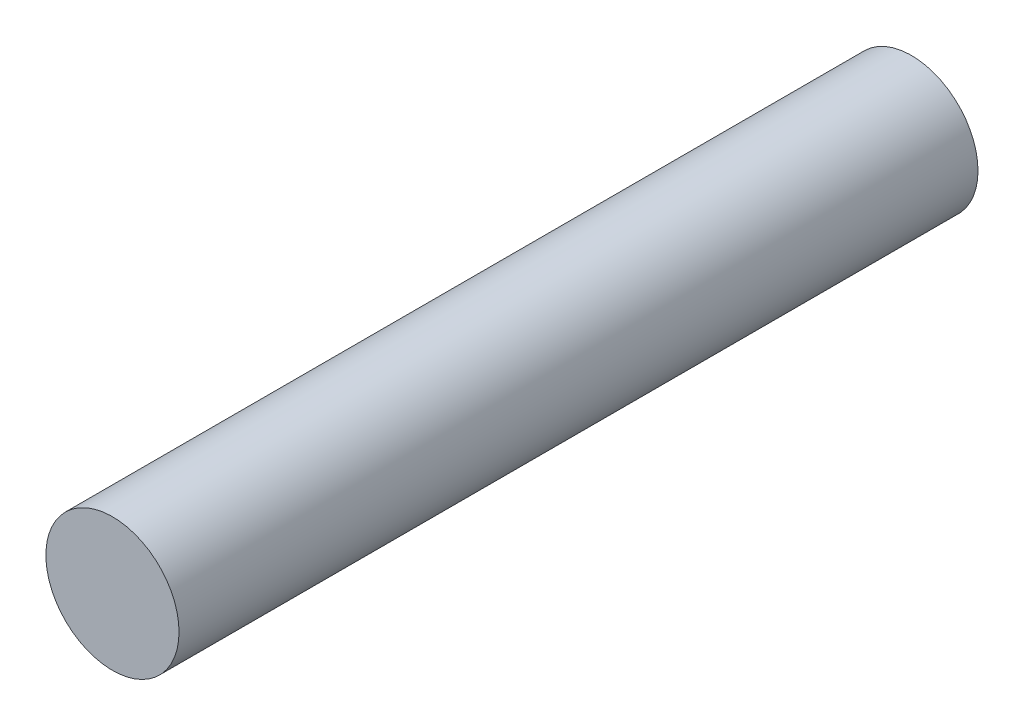
SolidWorks part; units mm, degrees
ref_plane "前基準面" through (0, 0, 0) normal (0, 0, 1) x (1, 0, 0)
ref_plane "上基準面" through (0, 0, 0) normal (0, 1, 0) x (1, 0, 0)
ref_plane "右基準面" through (0, 0, 0) normal (1, 0, 0) x (0, 0, -1)
sketch "草圖1" plane through (0, 0, 0) normal (0, 0, 1) x (1, 0, 0)
  circle A0 centre (0, 0) radius 2.5
  dimension "D1" = 5
extrude "填料-伸長1" add sketch "草圖1" along normal mid plane 30
